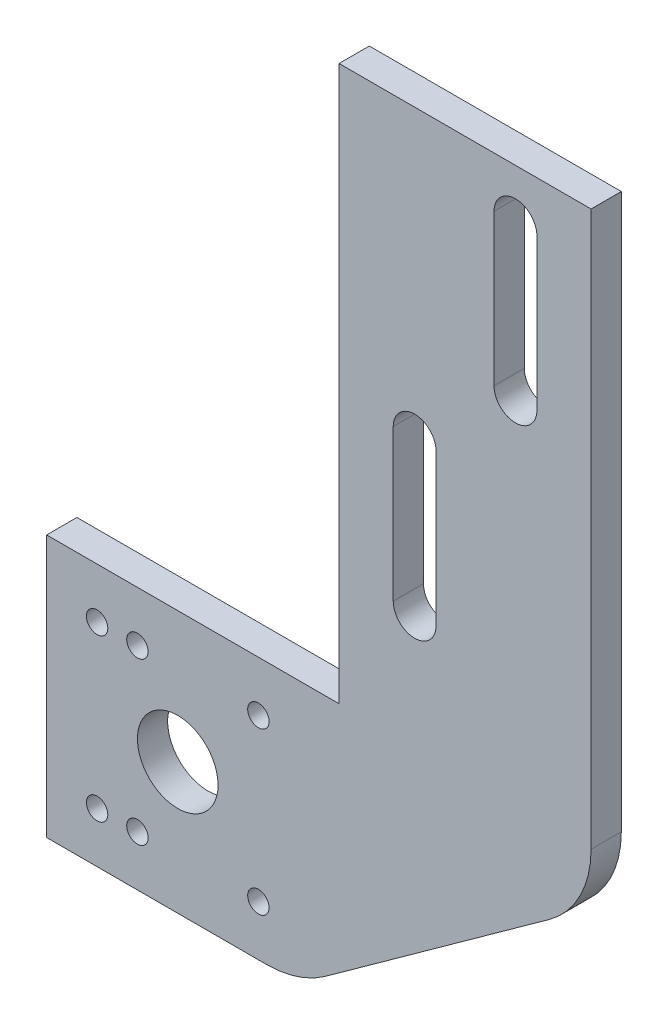
SolidWorks part; units mm, degrees
ref_plane "前视基准面" through (0, 0, 0) normal (0, 0, 1) x (1, 0, 0)
ref_plane "上视基准面" through (0, 0, 0) normal (0, 1, 0) x (1, 0, 0)
ref_plane "右视基准面" through (0, 0, 0) normal (1, 0, 0) x (0, 0, -1)
sketch "草图1" plane through (0, 0, 0) normal (0, 0, 1) x (1, 0, 0)
  line L0 (-12.39, -2.4348) -> (26.7705, -2.4348) construction
  line L1 (-12.39, -2.4348) -> (-12.39, 29.5652) construction
  line L2 (-22.39, -12.4348) -> (21.1597, -12.4348)
  line L3 (-22.39, -12.4348) -> (-22.39, 39.5652)
  line L4 (-22.39, 39.5652) -> (27.61, 39.5652)
  line L5 (27.61, -12.4348) -> (27.61, 39.5652) construction
  line L6 (-19.2366, 29.5652) -> (26.7705, 29.5652) construction
  line L7 (3.61, 29.5652) -> (3.61, -2.4348) construction
  line L8 (27.61, 39.5652) -> (35.61, 39.5652)
  line L9 (35.61, 149.5652) -> (85.61, 149.5652)
  line L10 (85.61, 149.5652) -> (85.61, 39.5652)
  line L11 (35.61, 39.5652) -> (35.61, 149.5652)
  line L12 (50.61, 92.5652) -> (50.61, 62.5652) construction
  line L13 (32.8448, -8.6662) -> (77.2951, 23.3338)
  line L14 (54.86, 92.5652) -> (54.86, 62.5652)
  line L15 (46.36, 92.5652) -> (46.36, 62.5652)
  line L16 (70.61, 109.5652) -> (70.61, 139.5652) construction
  line L17 (66.36, 109.5652) -> (66.36, 139.5652)
  line L18 (74.86, 109.5652) -> (74.86, 139.5652)
  circle A0 centre (-12.39, -2.4348) radius 2.125
  circle A1 centre (-4.39, -2.4348) radius 2.125
  circle A2 centre (3.61, -2.4348) radius 2.125 construction
  circle A3 centre (11.61, -2.4348) radius 2.125 construction
  circle A4 centre (19.61, -2.4348) radius 2.125
  circle A5 centre (-12.39, 29.5652) radius 2.125
  circle A6 centre (-4.39, 29.5652) radius 2.125
  circle A7 centre (3.61, 29.5652) radius 2.125 construction
  circle A8 centre (11.61, 29.5652) radius 2.125 construction
  circle A9 centre (19.61, 29.5652) radius 2.125
  circle A10 centre (3.61, 13.5652) radius 8
  arc A11 (21.1597, -12.4348) -> (32.8448, -8.6662) centre (21.1597, 7.5652) ccw
  arc A12 (85.61, 39.5652) -> (77.2951, 23.3338) centre (65.61, 39.5652) cw
  arc A13 (54.86, 92.5652) -> (46.36, 92.5652) centre (50.61, 92.5652) ccw
  arc A14 (46.36, 62.5652) -> (54.86, 62.5652) centre (50.61, 62.5652) ccw
  arc A15 (66.36, 109.5652) -> (74.86, 109.5652) centre (70.61, 109.5652) ccw
  arc A16 (74.86, 139.5652) -> (66.36, 139.5652) centre (70.61, 139.5652) ccw
  point P29 (50.61, 77.5652)
  point P45 (70.61, 124.5652)
  point P46 (7.1903, -2.4348)
  dimension "D1" = 4.25
  dimension "D5" = 4.25
  dimension "D8" = 32
  dimension "D9" = 16
  dimension "D10" = 8
  dimension "D14" = 20
  dimension "D3" = 10
  dimension "D4" = 32
  dimension "D7" = 10
  dimension "D11" = 8
  dimension "D12" = 110
  dimension "D13" = 50
  dimension "D15" = 8.5
  dimension "D16" = 65
  dimension "D17" = 10
  dimension "D18" = 30
  dimension "D19" = 15
  dimension "D20" = 8.5
  dimension "D21" = 15
  dimension "D22" = 30
  dimension "D23" = 10
  dimension "D2" = 5
  dimension "D6" = 5
extrude "凸台-拉伸1" add sketch "草图1" along normal blind 6
